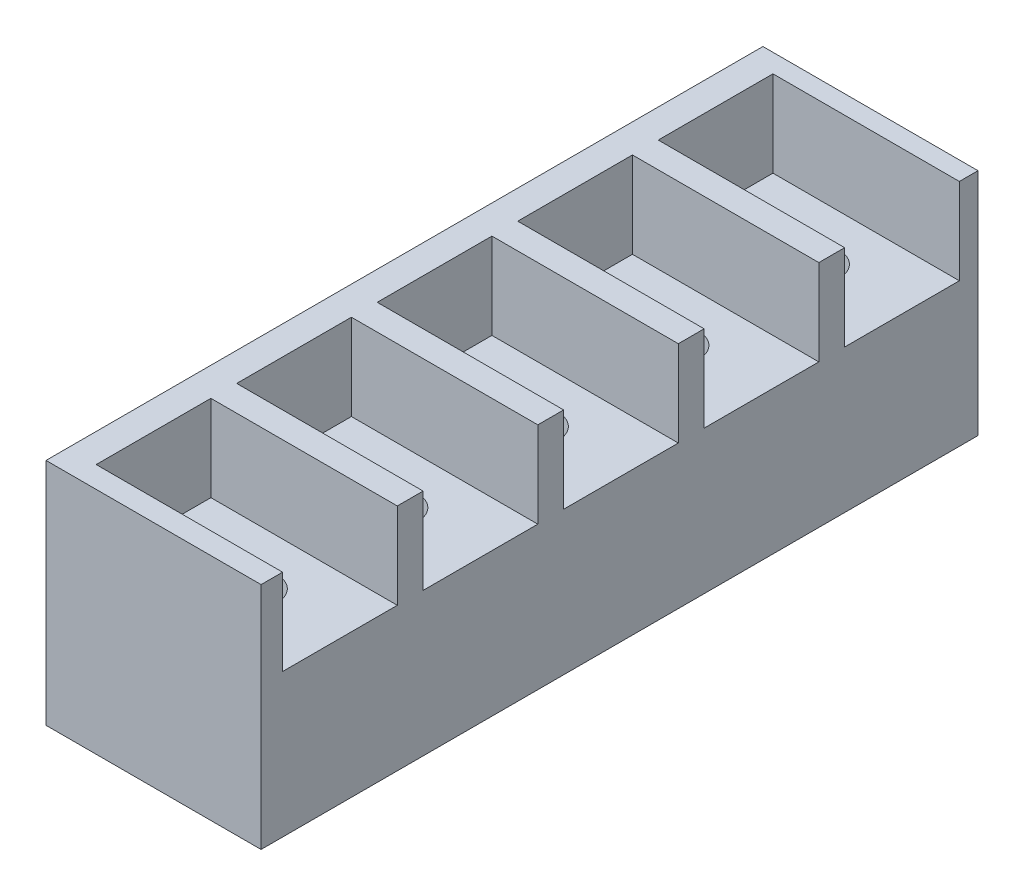
SolidWorks part; units mm, degrees
ref_plane "Front Plane" through (0, 0, 0) normal (0, 0, 1) x (1, 0, 0)
ref_plane "Top Plane" through (0, 0, 0) normal (0, 1, 0) x (1, 0, 0)
ref_plane "Right Plane" through (0, 0, 0) normal (1, 0, 0) x (0, 0, -1)
sketch "Sketch1" plane through (0, 0, 0) normal (0, 1, 0) x (1, 0, 0)
  line L1 (0, 0) -> (15, 0)
  line L2 (0, 0) -> (0, 50)
  line L3 (0, 50) -> (15, 50)
  line L4 (15, 0) -> (15, 50)
  dimension "D1" = 15
  dimension "D2" = 50
extrude "Boss-Extrude1" add sketch "Sketch1" along normal blind 16
sketch "Sketch2" plane through (0, 16, 0) normal (0, 1, 0) x (1, 0, 0)
  line L0 (15, 0) -> (15, 50) construction
  line L1 (15, 1.5) -> (2, 1.5)
  line L2 (15, 1.5) -> (15, 9.5)
  line L3 (15, 9.5) -> (2, 9.5)
  line L4 (2, 1.5) -> (2, 9.5)
  line L5 (0, 0) -> (15, 0) construction
  line L6 (15, 11.3) -> (15, 19.3)
  line L7 (15, 11.3) -> (2, 11.3)
  line L8 (2, 11.3) -> (2, 19.3)
  line L9 (15, 19.3) -> (2, 19.3)
  line L10 (15, 21.1) -> (15, 29.1)
  line L11 (15, 21.1) -> (2, 21.1)
  line L12 (2, 21.1) -> (2, 29.1)
  line L13 (15, 29.1) -> (2, 29.1)
  line L14 (15, 30.9) -> (15, 38.9)
  line L15 (15, 30.9) -> (2, 30.9)
  line L16 (2, 30.9) -> (2, 38.9)
  line L17 (15, 38.9) -> (2, 38.9)
  line L18 (15, 40.7) -> (15, 48.7)
  line L19 (15, 40.7) -> (2, 40.7)
  line L20 (2, 40.7) -> (2, 48.7)
  line L21 (15, 48.7) -> (2, 48.7)
  dimension "D1" = 1.5
  dimension "D2" = 13
  dimension "D3" = 8
  dimension "D4" = 5
extrude "Cut-Extrude1" cut sketch "Sketch2" against normal blind 6
sketch "Sketch5" plane through (0, 10, 0) normal (0, 1, 0) x (1, 0, 0)
  line L0 (9, 1.5) -> (9, 48.7) construction
  line L1 (2, 1.5) -> (15, 1.5) construction
  line L2 (15, 48.7) -> (2, 48.7) construction
  line L3 (15, 1.5) -> (15, 9.5) construction
  line L4 (2, 1.5) -> (15, 1.5) construction
  line L5 (2, 11.3) -> (15, 11.3) construction
  line L6 (2, 21.1) -> (15, 21.1) construction
  line L7 (2, 30.9) -> (15, 30.9) construction
  line L8 (2, 40.7) -> (15, 40.7) construction
  point P8 (9, 5.5)
  point P9 (9, 15.3)
  point P10 (9, 25.1)
  point P11 (9, 34.9)
  point P12 (9, 44.7)
  dimension "D1" = 6
  dimension "D2" = 4
  dimension "D3" = 4
  dimension "D4" = 4
  dimension "D5" = 4
  dimension "D6" = 4
hole_wizard "M4 Tapped Hole2" positions "Sketch6" profile "Sketch7" tap size "M4" standard "ISO"
sketch "Sketch6" plane through (0, 10, 0) normal (0, 1, 0) x (1, 0, 0)
  point P0 (9, 5.5)
  point P3 (9, 15.3)
  point P6 (9, 25.1)
  point P9 (9, 34.9)
  point P12 (9, 44.7)
sketch "Sketch7" plane through (9, 10, -5.5) normal (1, 0, 0) x (0, 0, 1)
  line L0 (0, 0) -> (0, 6.9914)
  line L1 (0, 6.9914) -> (1.65, 6)
  line L2 (1.65, 6) -> (1.65, 0)
  line L5 (1.65, 0) -> (0, 0)
  line L10 (0, 6.9914) -> (-1.65, 6) construction
  line L11 (0, -6.35) -> (0, 107.95) construction
  dimension "Tap Drill Dia." = 3.3
  dimension "Tap Drill Depth" = 6
  dimension "Drill Angle" = 118
cosmetic thread "Hole Thread10" parameters "D1"=6, "D2"=4
cosmetic thread "Hole Thread11" parameters "D1"=6, "D2"=4
cosmetic thread "Hole Thread12" parameters "D1"=6, "D2"=4
cosmetic thread "Hole Thread13" parameters "D1"=6, "D2"=4
cosmetic thread "Hole Thread14" parameters "D1"=6, "D2"=4
